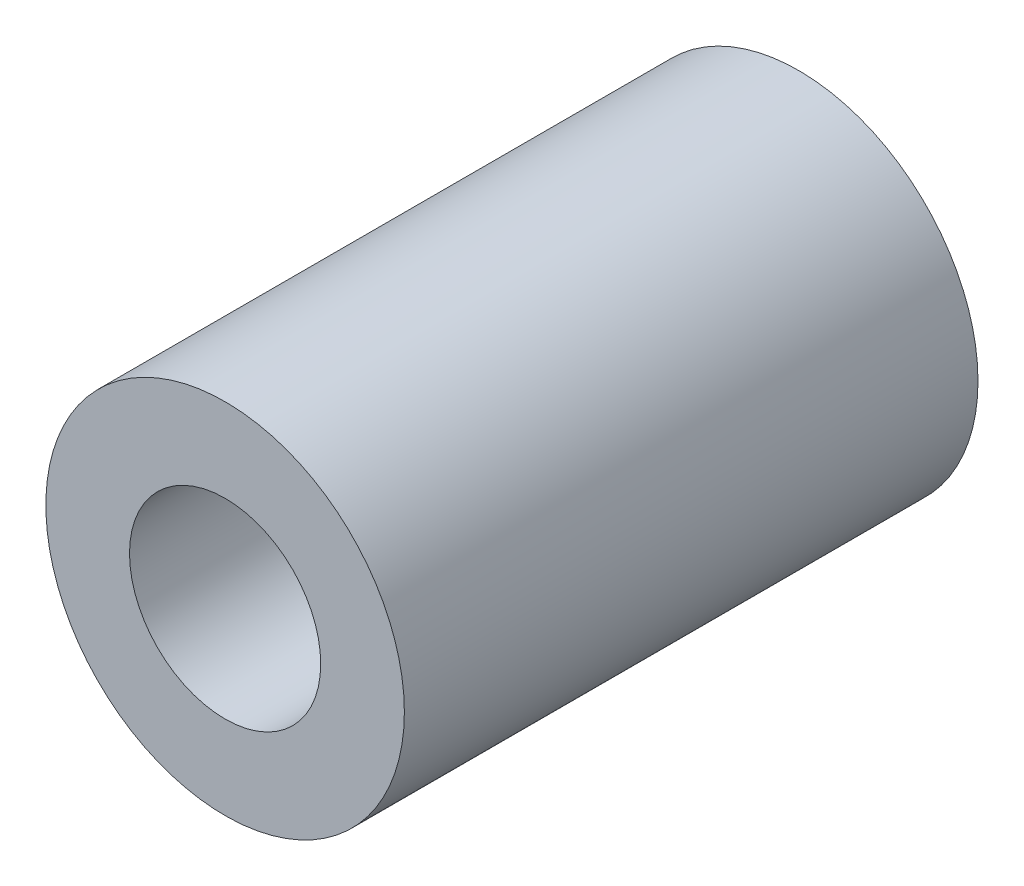
SolidWorks part; units mm, degrees
material "Plain Carbon Steel"
ref_plane "Front Plane" through (0, 0, 0) normal (0, 0, 1) x (1, 0, 0)
ref_plane "Top Plane" through (0, 0, 0) normal (0, 1, 0) x (1, 0, 0)
ref_plane "Right Plane" through (0, 0, 0) normal (1, 0, 0) x (0, 0, -1)
sketch "Sketch1" plane through (0, 0, 0) normal (0, 0, 1) x (1, 0, 0)
  circle A0 centre (0, 0) radius 7.5
  dimension "D1" = 15
extrude "Boss-Extrude1" add sketch "Sketch1" along normal blind 24
sketch "Sketch2" plane through (0, 0, 24) normal (0, 0, 1) x (1, 0, 0)
  circle A0 centre (0, 0) radius 4
  dimension "D1" = 8
extrude "Cut-Extrude1" cut sketch "Sketch2" against normal blind 24
